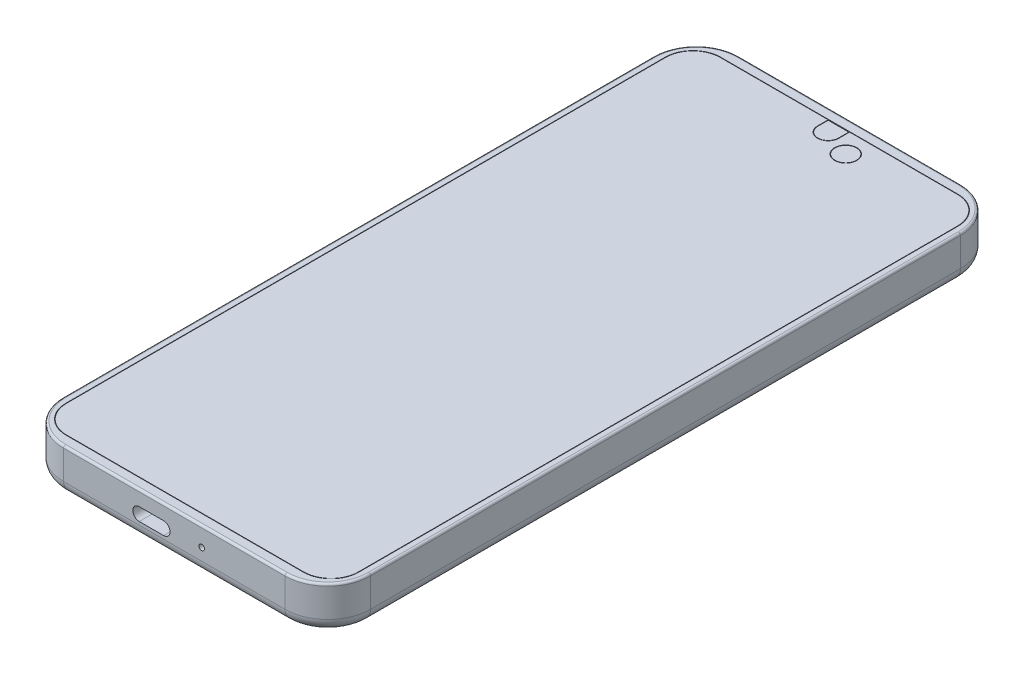
SolidWorks part; units mm, degrees
ref_plane "Ebene vorne" through (0, 0, 0) normal (0, 0, 1) x (1, 0, 0)
ref_plane "Ebene oben" through (0, 0, 0) normal (0, 1, 0) x (1, 0, 0)
ref_plane "Ebene rechts" through (0, 0, 0) normal (1, 0, 0) x (0, 0, -1)
sketch "Skizze1" plane through (0, 0, 0) normal (0, 1, 0) x (1, 0, 0)
  line L1 (-35.9, -79) -> (35.9, -79)
  line L2 (-35.9, -79) -> (-35.9, 79)
  line L3 (-35.9, 79) -> (35.9, 79)
  line L4 (35.9, -79) -> (35.9, 79)
  line L5 (0, 79) -> (0, -79) construction
  line L6 (-35.9, 0) -> (35.9, 0) construction
  point P0 (0, 0)
  dimension "D1" = 71.8
  dimension "D2" = 158
extrude "Aufsatz-Linear austragen1" add sketch "Skizze1" along normal blind 10.25
fillet "Verrundung1" radius 10 4 edges at (-35.9, 5.125, -79) (35.9, 5.125, -79) (-35.9, 5.125, 79) (35.9, 5.125, 79)
fillet "Verrundung2" radius 3 8 edges at (-32.9711, 0, 76.0711) (-35.9, 0, 0) (-32.9711, 0, -76.0711) (0, 0, -79) (32.9711, 0, -76.0711) (35.9, 0, 0) (32.9711, 0, 76.0711) (0, 0, 79)
fillet "Verrundung3" radius 0.5 8 edges at (-32.9711, 10.25, 76.0711) (-35.9, 10.25, 0) (-32.9711, 10.25, -76.0711) (0, 10.25, -79) (32.9711, 10.25, -76.0711) (35.9, 10.25, 0) (32.9711, 10.25, 76.0711) (0, 10.25, 79)
sketch "Skizze2" plane through (0, 10.25, 0) normal (0, 1, 0) x (1, 0, 0)
  line L1 (-27.75, 76.575) -> (27.75, 76.575)
  line L2 (-34.25, 70.075) -> (-34.25, -70.075)
  line L3 (-27.75, -76.575) -> (27.75, -76.575)
  line L4 (34.25, 70.075) -> (34.25, -70.075)
  line L5 (0, -76.575) -> (0, 76.575) construction
  line L6 (-34.25, 0) -> (34.25, 0) construction
  arc A0 (27.75, -76.575) -> (34.25, -70.075) centre (27.75, -70.075) ccw
  arc A1 (-34.25, -70.075) -> (-27.75, -76.575) centre (-27.75, -70.075) ccw
  arc A2 (27.75, 76.575) -> (34.25, 70.075) centre (27.75, 70.075) cw
  arc A3 (-27.75, 76.575) -> (-34.25, 70.075) centre (-27.75, 70.075) ccw
  point P0 (0, 0)
  point P8 (-34.25, -76.575)
  point P14 (-34.25, 76.575)
  dimension "D3" = 6.5
  dimension "D1" = 68.5
  dimension "D2" = 153.15
extrude "Schnitt-Linear-Austragen-Dünn1" cut sketch "Skizze2" against normal blind 0.5 thin
sketch "Skizze3" plane through (0, 10.25, 0) normal (0, 1, 0) x (1, 0, 0)
  line L0 (27.75, 76.475) -> (-27.75, 76.475) construction
  line L1 (-0.01, 71.475) -> (0.01, 71.475)
  line L2 (-2.5, 73.965) -> (-2.5, 76.475)
  line L3 (-2.5, 76.475) -> (2.5, 76.475)
  line L4 (2.5, 73.965) -> (2.5, 76.475)
  line L5 (0, 76.475) -> (0, 71.475) construction
  line L6 (-2.5, 75.22) -> (2.5, 75.22) construction
  arc A0 (0.01, 71.475) -> (2.5, 73.965) centre (0.01, 73.965) ccw
  arc A1 (-0.01, 71.475) -> (-2.5, 73.965) centre (-0.01, 73.965) cw
  point P0 (0, 75.22)
  point P8 (2.5, 71.475)
  point P12 (-2.5, 71.475)
  dimension "D3" = 2.49
  dimension "D1" = 5
  dimension "D2" = 5
extrude "Schnitt-Linear-Austragen-Dünn2" cut sketch "Skizze3" against normal blind 0.5 thin thin type one direction reverse wall 0.1
sketch "Skizze4" plane through (0, 10.25, 0) normal (0, 1, 0) x (1, 0, 0)
  line L0 (27.75, 76.575) -> (-27.75, 76.575) construction
  line L1 (2.5, 73.965) -> (2.5, 76.475) construction
  circle A0 centre (6.5, 71.575) radius 2.5
  dimension "D1" = 5
  dimension "D2" = 5
  dimension "D3" = 4
extrude "Schnitt-Linear-Austragen-Dünn3" cut sketch "Skizze4" against normal blind 0.5 thin
sketch "Skizze5" plane through (-35.9, 0, 0) normal (-1, 0, 0) x (0, 0, 1)
  line L0 (-36.1, 7.25) -> (-33.8, 7.25) construction
  line L1 (-45.7, 4.61) -> (-36.1, 4.61)
  line L2 (-47, 5.91) -> (-47, 5.95)
  line L3 (-45.7, 7.25) -> (-36.1, 7.25)
  line L4 (-36.1, 4.61) -> (-36.1, 7.25)
  line L5 (-40.9, 7.25) -> (-40.9, 4.61) construction
  line L6 (-47, 5.93) -> (-36.1, 5.93) construction
  line L7 (-24.2, 7.25) -> (-33.8, 7.25)
  line L8 (-22.9, 5.95) -> (-22.9, 5.91)
  line L9 (-24.2, 4.61) -> (-33.8, 4.61)
  line L10 (-33.8, 7.25) -> (-33.8, 4.61)
  line L11 (-29, 4.61) -> (-29, 7.25) construction
  line L12 (-22.9, 5.93) -> (-33.8, 5.93) construction
  line L13 (-5.5, 7.25) -> (-13.95, 7.25)
  line L14 (-4.2, 5.95) -> (-4.2, 5.91)
  line L15 (-5.5, 4.61) -> (-13.95, 4.61)
  line L16 (-15.25, 5.95) -> (-15.25, 5.91)
  line L17 (-9.725, 4.61) -> (-9.725, 7.25) construction
  line L18 (-4.2, 5.93) -> (-15.25, 5.93) construction
  line L19 (-22.9, 7.25) -> (-15.25, 7.25) construction
  line L20 (-36.1, 4.61) -> (-33.8, 4.61) construction
  line L21 (-22.9, 4.61) -> (-15.25, 4.61) construction
  line L22 (-69, 10.25) -> (69, 10.25) construction
  line L23 (-79, 3) -> (-79, 9.75) construction
  arc A0 (-4.2, 5.91) -> (-5.5, 4.61) centre (-5.5, 5.91) cw
  arc A1 (-5.5, 7.25) -> (-4.2, 5.95) centre (-5.5, 5.95) cw
  arc A2 (-13.95, 4.61) -> (-15.25, 5.91) centre (-13.95, 5.91) cw
  arc A3 (-13.95, 7.25) -> (-15.25, 5.95) centre (-13.95, 5.95) ccw
  arc A4 (-22.9, 5.91) -> (-24.2, 4.61) centre (-24.2, 5.91) cw
  arc A5 (-24.2, 7.25) -> (-22.9, 5.95) centre (-24.2, 5.95) cw
  arc A6 (-45.7, 4.61) -> (-47, 5.91) centre (-45.7, 5.91) cw
  arc A7 (-47, 5.95) -> (-45.7, 7.25) centre (-45.7, 5.95) cw
  point P0 (-40.9, 5.93)
  point P4 (-29, 5.93)
  point P8 (-9.725, 5.93)
  point P36 (-47, 7.25)
  dimension "D8" = 1.3
  dimension "D1" = 10.9
  dimension "D2" = 11.05
  dimension "D3" = 2.64
  dimension "D4" = 3
  dimension "D5" = 32
  dimension "D6" = 2.3
  dimension "D7" = 7.65
extrude "Aufsatz-Linear austragen2" add sketch "Skizze5" along normal blind 0.5
sketch "Skizze6" plane through (0, 0, -79) normal (0, 0, -1) x (-1, 0, 0)
  line L0 (35.9, 9.75) -> (35.9, 3) construction
  line L1 (25.9, 0) -> (-25.9, 0) construction
  circle A0 centre (23.4, 4.55) radius 1.875
  circle A1 centre (12.4, 6) radius 0.65
  dimension "D1" = 3.75
  dimension "D4" = 1.3
  dimension "D2" = 12.5
  dimension "D3" = 4.55
  dimension "D5" = 6
  dimension "D6" = 23.5
extrude "Schnitt-Linear austragen1" cut sketch "Skizze6" against normal blind 25
sketch "Skizze7" plane through (0, 0, 79) normal (0, 0, 1) x (1, 0, 0)
  line L0 (-8.2, 5.25) -> (-2.5, 5.25) construction
  line L1 (-8.2, 6.75) -> (-2.5, 6.75)
  line L2 (-8.2, 3.75) -> (-2.5, 3.75)
  line L3 (35.9, 9.75) -> (35.9, 3) construction
  line L4 (-25.9, 10.25) -> (25.9, 10.25) construction
  line L6 (25.9, 0) -> (-25.9, 0) construction
  circle A0 centre (6.4, 5.8) radius 0.65
  arc A1 (-8.2, 6.75) -> (-8.2, 3.75) centre (-8.2, 5.25) ccw
  arc A2 (-2.5, 3.75) -> (-2.5, 6.75) centre (-2.5, 5.25) ccw
  point P4 (-5.35, 5.25)
  point P9 (-9.7, 5.25)
  point P10 (-1, 5.25)
  point P15 (0, 0)
  dimension "D1" = 1.3
  dimension "D3" = 8.7
  dimension "D2" = 3
  dimension "D4" = 36.9
  dimension "D5" = 3.5
  dimension "D6" = 5.8
  dimension "D7" = 29.5
extrude "Schnitt-Linear austragen2" cut sketch "Skizze7" against normal blind 7
sketch "Skizze8" plane through (0, 0, 0) normal (0, -1, 0) x (1, 0, 0)
  line L0 (25.9, -79) -> (-22.345, -79) construction
  circle A0 centre (0, -55.5) radius 5.25
  point P4 (0, 0)
  dimension "D1" = 10.5
  dimension "D2" = 23.5
extrude "Schnitt-Linear austragen3" cut sketch "Skizze8" against normal blind 0.9
chamfer "Fase1" distance 0.8 angle 45 1 edges at (0, 0, -60.75)
sketch "Skizze9" plane through (0, 0, 0) normal (0, -1, 0) x (1, 0, 0)
  line L0 (25.4, -69) -> (16.5, -69) construction
  line L1 (25.4, -74.5) -> (16.5, -74.5)
  line L2 (25.4, -63.5) -> (16.5, -63.5)
  line L3 (25.9, -79) -> (-22.345, -79) construction
  line L4 (35.9, 69) -> (35.9, -69) construction
  arc A0 (25.4, -74.5) -> (25.4, -63.5) centre (25.4, -69) ccw
  arc A1 (16.5, -63.5) -> (16.5, -74.5) centre (16.5, -69) ccw
  point P2 (20.95, -69)
  point P7 (30.9, -69)
  point P8 (11, -69)
  dimension "D1" = 11
  dimension "D2" = 19.9
  dimension "D3" = 4.5
  dimension "D4" = 5
extrude "Schnitt-Linear austragen4" cut sketch "Skizze9" against normal blind 0.3
chamfer "Fase2" distance 0.2 angle 45 4 edges at (20.95, 0, -74.5) (30.9, 0, -69) (11, 0, -69) (20.95, 0, -63.5)
